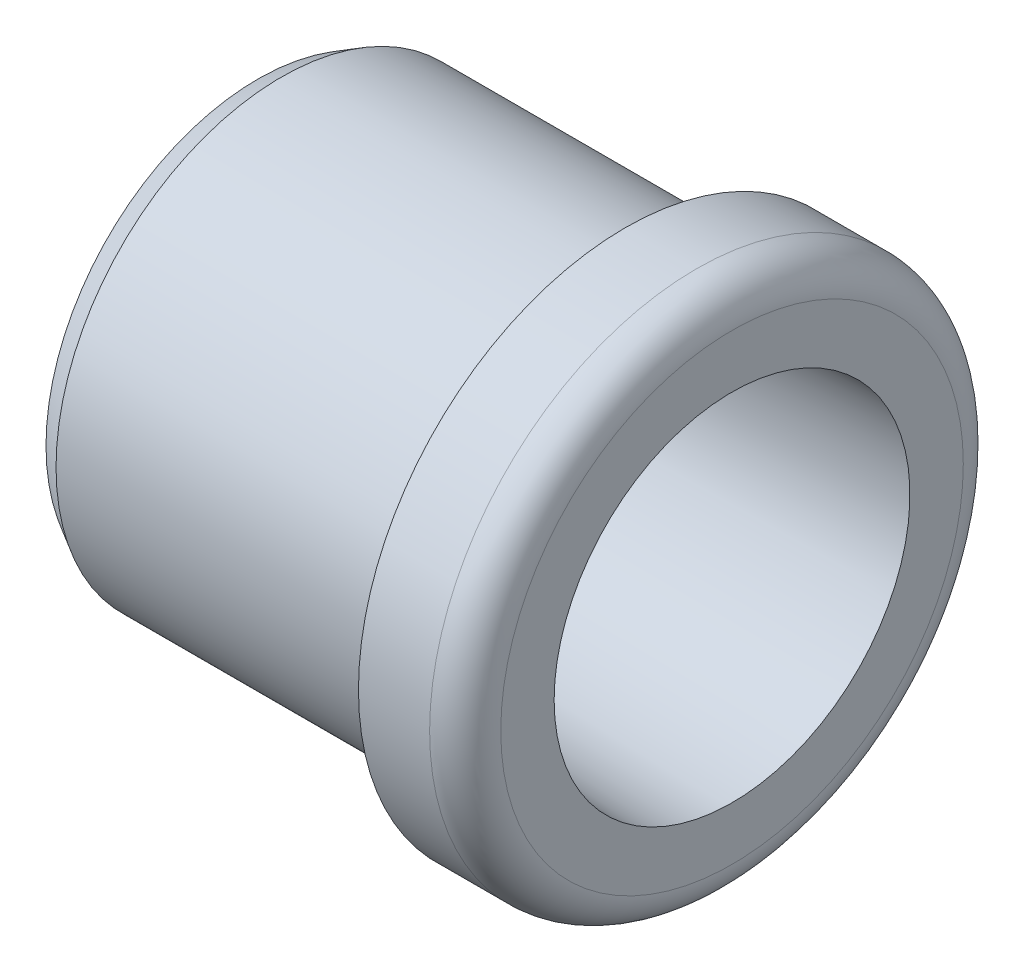
SolidWorks part; units mm, degrees
ref_plane "Plane1" through (0, 0, 0) normal (0, 0, 1) x (1, 0, 0)
ref_plane "Plane2" through (0, 0, 0) normal (0, 1, 0) x (1, 0, 0)
ref_plane "Plane3" through (0, 0, 0) normal (1, 0, 0) x (0, 0, -1)
sketch "Sketch1" plane through (0, 0, 0) normal (0, 0, 1) x (1, 0, 0)
  line L0 (0, 0) -> (80.4003, 0) construction
  line L1 (0, 17.8453) -> (2, 19)
  line L3 (40, 15) -> (40, 19.5)
  line L4 (37, 22.5) -> (31, 22.5)
  line L5 (31, 22.5) -> (31, 19)
  line L6 (31, 19) -> (2, 19)
  line L7 (0, 17.8453) -> (0, 5.1)
  line L8 (12, 13.2497) -> (12, 5.1)
  line L9 (12.7721, 14.0492) -> (40, 15)
  line L10 (0, 5.1) -> (12, 5.1)
  arc A0 (40, 19.5) -> (37, 22.5) centre (37, 19.5) ccw
  arc A1 (12, 13.2497) -> (12.7721, 14.0492) centre (12.8, 13.2497) cw
  dimension "D11" = 3
  dimension "D9" = 0.8
  dimension "D2" = 31
  dimension "D3" = 38
  dimension "D4" = 45
  dimension "D5" = 28
  dimension "D6" = 30
  dimension "D7" = 40
  dimension "D8" = 2
  dimension "D10" = 10.2
  dimension "D12" = 30
  dimension "D13" = 2
revolve "Revolve1" add sketch "Sketch1" angle 360 about L0
cosmetic thread "Cosmetic Thread1"
